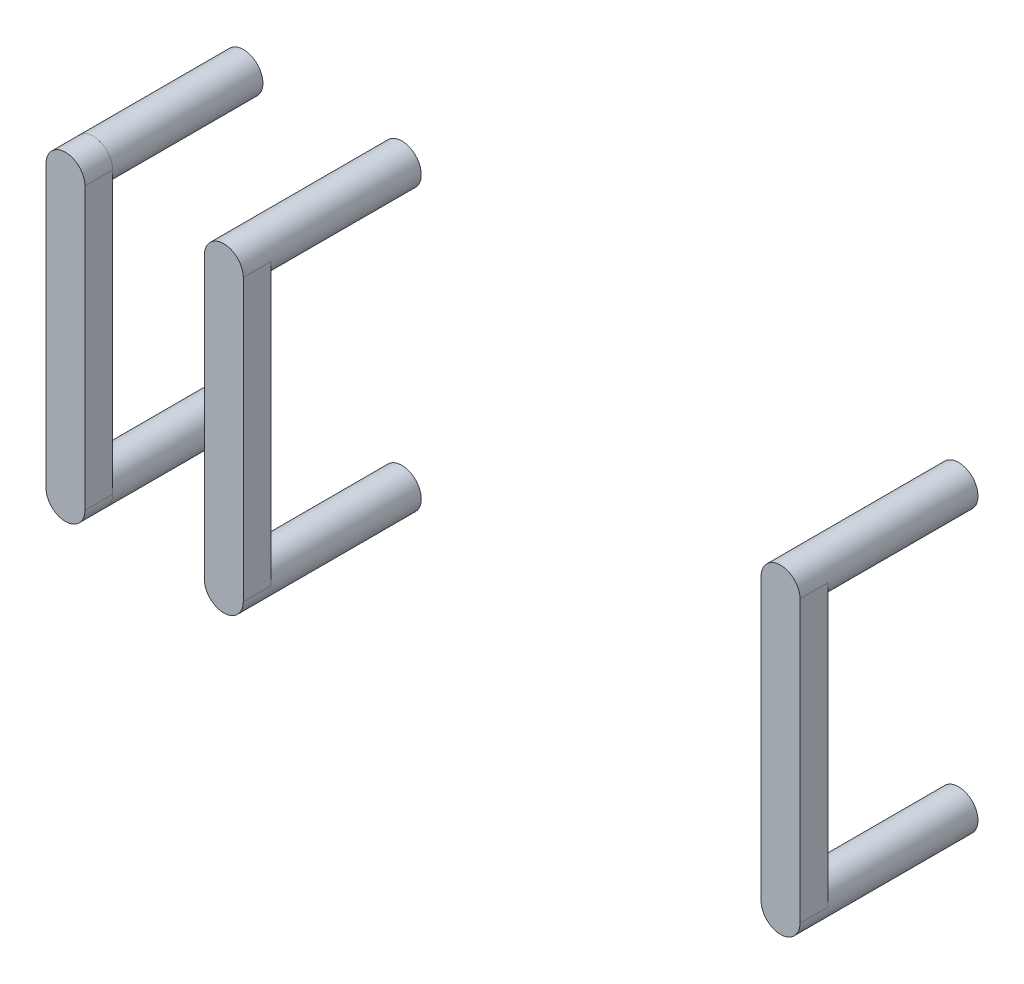
SolidWorks part; units mm, degrees
ref_plane "Ebene vorne" through (0, 0, 0) normal (0, 0, 1) x (1, 0, 0)
ref_plane "Ebene oben" through (0, 0, 0) normal (0, 1, 0) x (1, 0, 0)
ref_plane "Ebene rechts" through (0, 0, 0) normal (1, 0, 0) x (0, 0, -1)
sketch "Skizze1" plane through (0, 0, 0) normal (0, 0, 1) x (1, 0, 0)
  line L0 (0, 0) -> (0, -95) construction
  line L1 (-16.5833, -95) -> (16.5833, -95) construction
  line L2 (-74.55, -54.95) -> (74.55, -54.95) construction
  line L3 (-74.55, -80.2019) -> (-50.05, -80.2019) construction
  line L4 (74.55, -80.2019) -> (74.55, -29.6981) construction
  line L5 (-64.2875, -33.6889) -> (-64.2875, -62.9948) construction
  line L6 (-82.5, -29.6981) -> (-74.55, -29.6981) construction
  line L7 (-82.5, 85) -> (-82.5, -85) construction
  line L8 (-74.55, -29.6981) -> (-74.55, -80.2019) construction
  circle A0 centre (-50.05, -80.2019) radius 3.5
  circle A1 centre (50.05, -80.2019) radius 3.5
  circle A2 centre (50.05, -29.6981) radius 3.5
  circle A3 centre (-50.05, -29.6981) radius 3.5
  circle A4 centre (-78.525, -80.2019) radius 3.5
  circle A5 centre (-78.525, -29.6981) radius 3.5
  spline S3 degree 3 poles (-53.55, -80.2019) (-53.55, -80.8972) (-53.6613, -81.5753) (-54.0078, -82.5587) (-54.1506, -82.8711) (-54.4907, -83.4651) (-54.6889, -83.7476) (-55.1431, -84.2741) (-55.3922, -84.5104) (-55.799, -84.8243) (-55.9402, -84.9221) (-56.2342, -85.1034) (-56.3881, -85.1873) (-56.8565, -85.4105) (-57.1805, -85.5237) (-57.852, -85.6778) (-58.2011, -85.7181) (-58.55, -85.7181) knots 0 0 0 0 0.25 0.25 0.375 0.375 0.5 0.5 0.625 0.625 0.6875 0.6875 0.75 0.75 0.875 0.875 1 1 1 1 construction
  dimension "D1" = 7
extrude "Aufsatz-Linear austragen1" add sketch "Skizze1" along normal up to surface (27 mm away)
sketch "Skizze2" plane through (0, 0, 0) normal (0, 0, -1) x (-1, 0, 0)
  line L0 (4.1549, -54.95) -> (0, -54.95) construction
  line L1 (0, -54.95) -> (0, -21.9995) construction
  circle A0 centre (50.05, -80.2019) radius 2.1
  circle A1 centre (50.05, -29.6981) radius 2.1
  circle A2 centre (-50.05, -29.6981) radius 2.1
  circle A3 centre (-50.05, -80.2019) radius 2.1
  circle A4 centre (-50.05, -29.6981) radius 3.5 construction
  dimension "D1" = 4.2
extrude "Schnitt-Linear austragen1" cut sketch "Skizze2" against normal blind 5.7
sketch "Skizze4" plane through (0, 0, 27) normal (0, 0, 1) x (1, 0, 0)
  line L0 (-53.55, -80.2019) -> (-53.55, -29.6981)
  line L1 (-46.55, -29.6981) -> (-46.55, -80.2019)
  line L2 (-53.55, -80.2019) -> (-46.55, -80.2019) construction
  line L3 (0, -95) -> (0, -135.4882) construction
  line L4 (53.55, -80.2019) -> (46.55, -80.2019) construction
  line L5 (46.55, -29.6981) -> (46.55, -80.2019)
  line L6 (53.55, -80.2019) -> (53.55, -29.6981)
  line L7 (-16.5833, -95) -> (16.5833, -95) construction
  line L8 (-64.2875, -28.2085) -> (-64.2875, -66.3006) construction
  line L9 (-75.025, -80.2019) -> (-82.025, -80.2019) construction
  line L10 (-82.025, -29.6981) -> (-82.025, -80.2019)
  line L11 (-75.025, -80.2019) -> (-75.025, -29.6981)
  arc A0 (-53.55, -80.2019) -> (-46.55, -80.2019) centre (-50.05, -80.2019) ccw
  circle A1 centre (-50.05, -80.2019) radius 3.5 construction
  arc A2 (-53.55, -29.6981) -> (-46.55, -29.6981) centre (-50.05, -29.6981) cw
  circle A3 centre (-50.05, -29.6981) radius 3.5 construction
  arc A4 (53.55, -29.6981) -> (46.55, -29.6981) centre (50.05, -29.6981) ccw
  arc A5 (53.55, -80.2019) -> (46.55, -80.2019) centre (50.05, -80.2019) cw
  arc A6 (-75.025, -29.6981) -> (-82.025, -29.6981) centre (-78.525, -29.6981) ccw
  arc A7 (-75.025, -80.2019) -> (-82.025, -80.2019) centre (-78.525, -80.2019) cw
  circle A8 centre (-78.525, -29.6981) radius 3.5 construction
extrude "Aufsatz-Linear austragen2" add sketch "Skizze4" along normal blind 5
equation "\"M2EinschmelzGewindeDurchmesser\"=3.4"
equation "\"M2EinschmelzGewindeTiefe\"= 4.0"
equation "\"M3EinschmelzGewindeDurchmesser\"= 4.2"
equation "\"M3EinschmelzGewindeTief\"= 5.7"
equation "\"M2SchraubeLoch\"=2.3"
equation "\"M3SchraubeLoch\"=3.3"
equation "\"offSetVonGummiReifen\"= 3.0"
equation "\"D1@Skizze2\"=\"M3EinschmelzGewindeDurchmesser\""
equation "\"D1@Schnitt-Linear austragen1\"=\"M3EinschmelzGewindeTief\""
